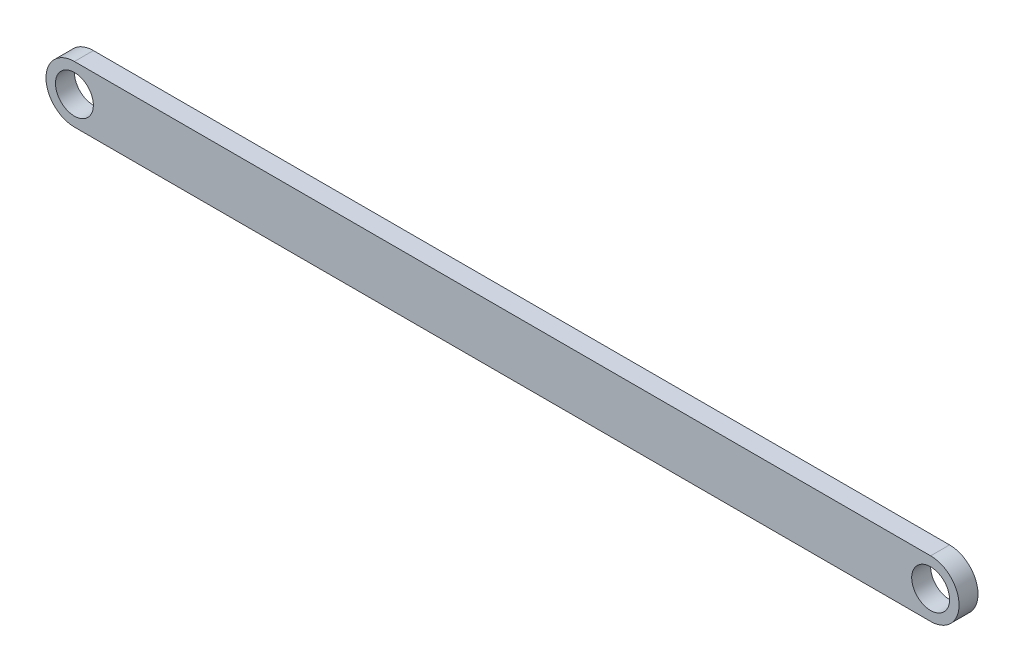
SolidWorks part; units mm, degrees
ref_plane "Front Plane" through (0, 0, 0) normal (0, 0, 1) x (1, 0, 0)
ref_plane "Top Plane" through (0, 0, 0) normal (0, 1, 0) x (1, 0, 0)
ref_plane "Right Plane" through (0, 0, 0) normal (1, 0, 0) x (0, 0, -1)
other "Center of Mass"
sketch "Sketch1" plane through (0, 0, 0) normal (0, 0, 1) x (1, 0, 0)
  line L0 (-95.201, 0) -> (145.799, 0)
  line L1 (145.799, 0) -> (145.799, 15)
  line L2 (145.799, 15) -> (-95.201, 15)
  line L3 (-95.201, 15) -> (-95.201, 0)
  dimension "D1" = 241
  dimension "D2" = 15
extrude "Boss-Extrude1" add sketch "Sketch1" along normal blind 5
sketch "Sketch2" plane through (0, 0, 5) normal (0, 0, 1) x (1, 0, 0)
  line L0 (-95.201, 7.5) -> (145.799, 7.5) construction
  line L1 (-95.201, 15) -> (-95.201, 0) construction
  line L2 (145.799, 0) -> (145.799, 15) construction
  line L3 (25.299, 15) -> (25.299, -7.6611) construction
  line L4 (145.799, 15) -> (-95.201, 15) construction
  line L9 (-95.201, 15) -> (-95.201, 0)
  line L10 (-95.201, 0) -> (145.799, 0)
  line L11 (145.799, 0) -> (145.799, 15)
  line L12 (145.799, 15) -> (-95.201, 15)
  line L13 (-95.201, 15) -> (-95.201, 0)
  line L14 (-95.201, 0) -> (145.799, 0)
  line L15 (145.799, 0) -> (145.799, 15)
  line L16 (145.799, 15) -> (-95.201, 15)
  circle A0 centre (-87.701, 7.5) radius 7.5
  circle A1 centre (-87.701, 7.5) radius 5
  circle A2 centre (138.299, 7.5) radius 7.5
  circle A3 centre (138.299, 7.5) radius 5
  line M7 (-95.201, 15) -> (-95.201, 0)
  line M8 (-95.201, 0) -> (145.799, 0)
  line M9 (145.799, 0) -> (145.799, 15)
  line M10 (145.799, 15) -> (-95.201, 15)
  dimension "D1" = 15
  dimension "D3" = 0
  dimension "D2" = 7.5
extrude "Cut-Extrude2" cut sketch "Sketch2" against normal blind 5 contours A1 | A0 L16 M7 | A0 L13 M8 | A3 | A2 L15 M10 | A2 M9 M8
